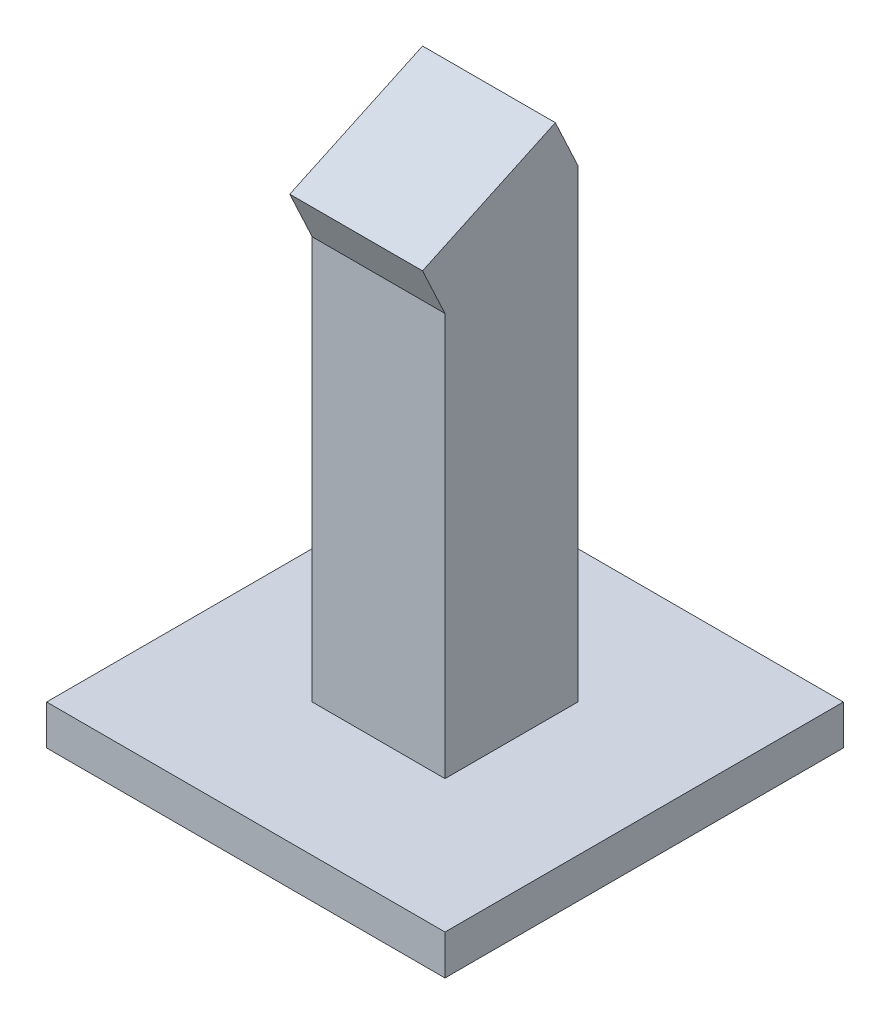
SolidWorks part; units mm, degrees
ref_plane "Front Plane" through (0, 0, 0) normal (0, 0, 1) x (1, 0, 0)
ref_plane "Top Plane" through (0, 0, 0) normal (0, 1, 0) x (1, 0, 0)
ref_plane "Right Plane" through (0, 0, 0) normal (1, 0, 0) x (0, 0, -1)
sketch "Sketch1" plane through (0, 0, 0) normal (0, 1, 0) x (1, 0, 0)
  line L1 (0, 0) -> (30, 0)
  line L2 (0, 0) -> (0, -30)
  line L3 (0, -30) -> (30, -30)
  line L4 (30, 0) -> (30, -30)
  point P4 (0, 0)
  dimension "D1" = 30
  dimension "D2" = 30
extrude "Boss-Extrude1" add sketch "Sketch1" along normal blind 3
sketch "Sketch2" plane through (0, 3, 0) normal (0, 1, 0) x (1, 0, 0)
  line L0 (0, 0) -> (0, -30) construction
  line L1 (10, -10) -> (20, -10)
  line L2 (10, -10) -> (10, -20)
  line L3 (10, -20) -> (20, -20)
  line L4 (20, -10) -> (20, -20)
  line L5 (30, 0) -> (0, 0) construction
  point P4 (9.5137, -9.7568)
  dimension "D1" = 10
  dimension "D2" = 10
  dimension "D3" = 10
  dimension "D4" = 10
extrude "Boss-Extrude2" add sketch "Sketch2" along normal blind 35
sketch "Sketch3" plane through (20, 0, 0) normal (1, 0, 0) x (0, 0, -1)
  line L0 (-20, 38) -> (-10, 38)
  line L1 (-10, 38) -> (-20, 33.3369)
  line L2 (-20, 38) -> (-20, 3) construction
  line L3 (-20, 33.3369) -> (-20, 38)
  dimension "D1" = 25
extrude "Cut-Extrude2" cut sketch "Sketch3" against normal through all
sketch "Sketch5" plane through (0, 35.0432, 16.3409) normal (0, 0.9063, 0.4226) x (1, 0, 0)
  line L1 (10, 6.9964) -> (20, 6.9964)
  line L2 (10, 6.9964) -> (10, -4.0374)
  line L3 (10, -4.0374) -> (20, -4.0374)
  line L4 (20, 6.9964) -> (20, -4.0374)
extrude "Boss-Extrude3" add sketch "Sketch5" along normal blind 4
